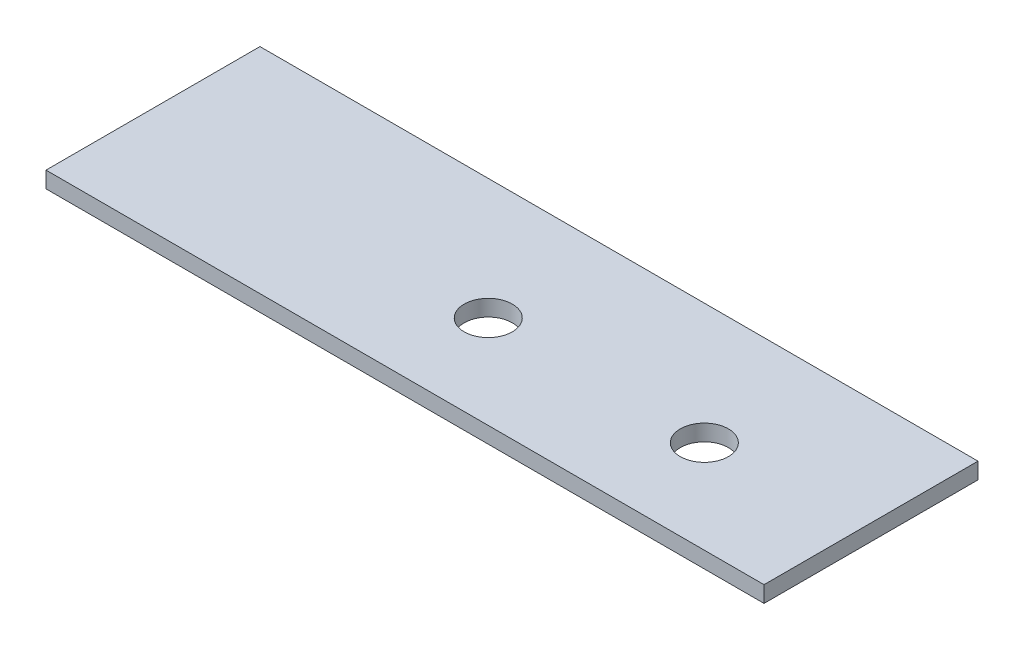
SolidWorks part; units mm, degrees
ref_plane "Front Plane" through (0, 0, 0) normal (0, 0, 1) x (1, 0, 0)
ref_plane "Top Plane" through (0, 0, 0) normal (0, 1, 0) x (1, 0, 0)
ref_plane "Right Plane" through (0, 0, 0) normal (1, 0, 0) x (0, 0, -1)
sketch "Sketch1" plane through (0, 0, 0) normal (0, 1, 0) x (1, 0, 0)
  line L1 (-16.78, 5) -> (16.78, 5)
  line L2 (-16.78, 5) -> (-16.78, -5)
  line L3 (-16.78, -5) -> (16.78, -5)
  line L4 (16.78, 5) -> (16.78, -5)
  line L5 (-16.78, 5) -> (16.78, -5) construction
  line L6 (-16.78, -5) -> (16.78, 5) construction
  circle A0 centre (-21.78, 0) radius 1.75 construction
  circle A4 centre (-0.46, -0.65) radius 1.125
  circle A5 centre (9.64, -0.65) radius 1.125
  point P0 (0, 0)
  dimension "D5" = 5
  dimension "D6" = 21.32
  dimension "D10" = 2.25
  dimension "D11" = 2.25
  dimension "D4" = 3.5
  dimension "D1" = 10
  dimension "D2" = 33.56
  dimension "D3" = 0.65
  dimension "D12" = 10.1
extrude "Boss-Extrude1" add sketch "Sketch1" along normal mid plane 0.76
